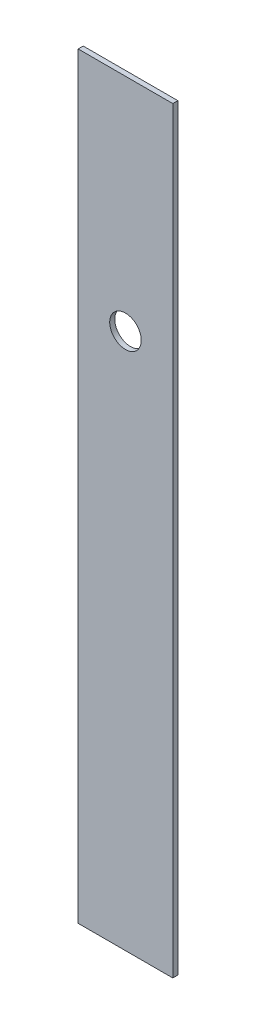
SolidWorks part; units mm, degrees
ref_plane "Front Plane" through (0, 0, 0) normal (0, 0, 1) x (1, 0, 0)
ref_plane "Top Plane" through (0, 0, 0) normal (0, 1, 0) x (1, 0, 0)
ref_plane "Right Plane" through (0, 0, 0) normal (1, 0, 0) x (0, 0, -1)
sketch "Sketch1" plane through (0, 0, 0) normal (0, 0, 1) x (1, 0, 0)
  line L1 (-9.525, 0) -> (9.525, 0)
  line L2 (-9.525, 0) -> (-9.525, 152.4)
  line L3 (-9.525, 152.4) -> (9.525, 152.4)
  line L4 (9.525, 0) -> (9.525, 152.4)
  point P4 (0, 0)
  dimension "D1" = 19.05
  dimension "D2" = 152.4
extrude "Boss-Extrude1" add sketch "Sketch1" along normal blind 1.016
sketch "Sketch2" plane through (0, 0, 1.016) normal (0, 0, 1) x (1, 0, 0)
  line L0 (9.525, 152.4) -> (-9.525, 152.4) construction
  circle A0 centre (0, 107.95) radius 3.175
  point P2 (0, 0)
  dimension "D1" = 6.35
  dimension "D2" = 44.45
extrude "Cut-Extrude1" cut sketch "Sketch2" against normal through all
